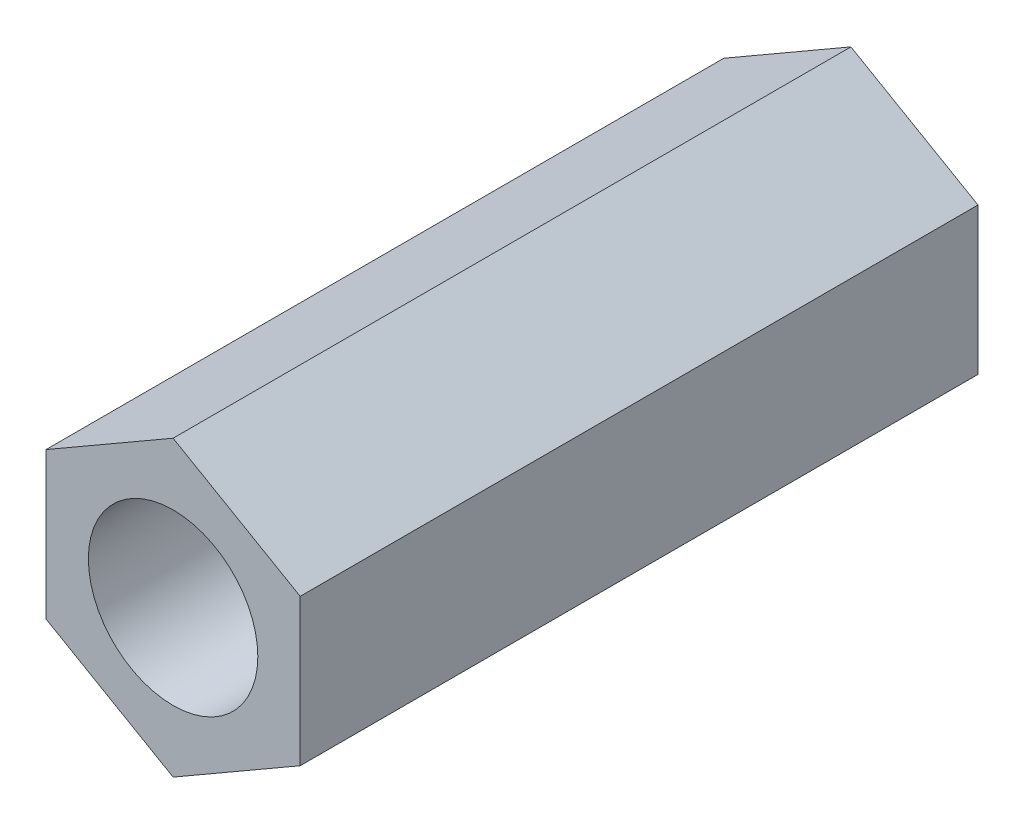
SolidWorks part; units mm, degrees
ref_plane "Front Plane" through (0, 0, 0) normal (0, 0, 1) x (1, 0, 0)
ref_plane "Top Plane" through (0, 0, 0) normal (0, 1, 0) x (1, 0, 0)
ref_plane "Right Plane" through (0, 0, 0) normal (1, 0, 0) x (0, 0, -1)
sketch "Sketch1" plane through (0, 0, 0) normal (0, 0, 1) x (1, 0, 0)
  line L1 (14.2875, -8.2489) -> (14.2875, 8.2489)
  line L2 (14.2875, 8.2489) -> (0, 16.4978)
  line L3 (0, 16.4978) -> (-14.2875, 8.2489)
  line L4 (-14.2875, 8.2489) -> (-14.2875, -8.2489)
  line L5 (-14.2875, -8.2489) -> (0, -16.4978)
  line L6 (0, -16.4978) -> (14.2875, -8.2489)
  circle A0 centre (0, 0) radius 14.2875 construction
  circle A1 centre (0, 0) radius 9.525
  point P1 (14.2875, 0)
  dimension "D2" = 19.05
  dimension "D1" = 28.575
extrude "Boss-Extrude1" add sketch "Sketch1" along normal blind 76.2
